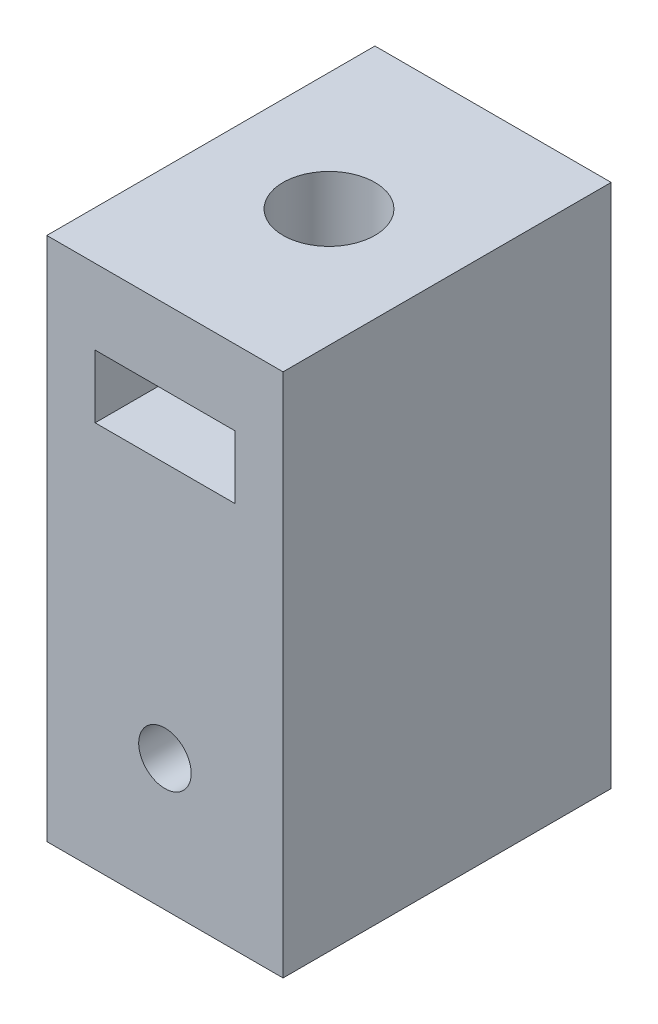
SolidWorks part; units mm, degrees
ref_plane "Front Plane" through (0, 0, 0) normal (0, 0, 1) x (1, 0, 0)
ref_plane "Top Plane" through (0, 0, 0) normal (0, 1, 0) x (1, 0, 0)
ref_plane "Right Plane" through (0, 0, 0) normal (1, 0, 0) x (0, 0, -1)
sketch "Sketch1" plane through (0, 0, 0) normal (0, 1, 0) x (1, 0, 0)
  line L1 (-4.5, -6.25) -> (4.5, -6.25)
  line L2 (-4.5, -6.25) -> (-4.5, 6.25)
  line L3 (-4.5, 6.25) -> (4.5, 6.25)
  line L4 (4.5, -6.25) -> (4.5, 6.25)
  line L5 (-4.5, -6.25) -> (4.5, 6.25) construction
  line L6 (-4.5, 6.25) -> (4.5, -6.25) construction
  point P0 (0, 0)
  dimension "D1" = 12.5
  dimension "D2" = 9
extrude "Boss-Extrude1" add sketch "Sketch1" along normal blind 20
sketch "Sketch2" plane through (0, 0, 6.25) normal (0, 0, 1) x (1, 0, 0)
  line L0 (-4.5, 0) -> (4.5, 0) construction
  circle A0 centre (0, 5) radius 1
  dimension "D2" = 2
  dimension "D1" = 5
extrude "Cut-Extrude1" cut sketch "Sketch2" against normal through all
sketch "Sketch3" plane through (0, 0, 6.25) normal (0, 0, 1) x (1, 0, 0)
  line L0 (-4.5, 20) -> (4.5, 20) construction
  line L1 (-2.66, 17.1376) -> (2.66, 17.1376)
  line L2 (-2.66, 17.1376) -> (-2.66, 14.7376)
  line L3 (-2.66, 14.7376) -> (2.66, 14.7376)
  line L4 (2.66, 17.1376) -> (2.66, 14.7376)
  point P4 (0, 17.1376)
  point P7 (0, 20)
  dimension "D1" = 5.32
  dimension "D2" = 2.4
extrude "Cut-Extrude2" cut sketch "Sketch3" against normal through all
sketch "Sketch4" plane through (0, 20, 0) normal (0, 1, 0) x (1, 0, 0)
  circle A0 centre (0, 0) radius 1.75
  dimension "D1" = 3.5
extrude "Cut-Extrude3" cut sketch "Sketch4" against normal blind 13
